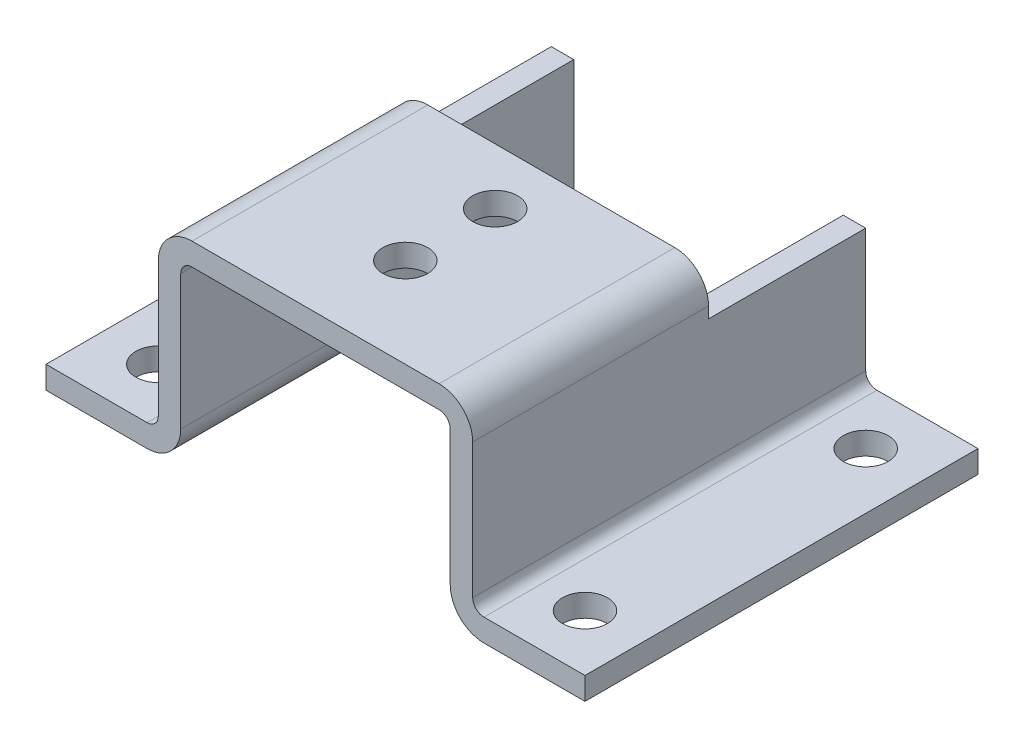
SolidWorks part; units mm, degrees
ref_plane "Front Plane" through (0, 0, 0) normal (0, 0, 1) x (1, 0, 0)
ref_plane "Top Plane" through (0, 0, 0) normal (0, 1, 0) x (1, 0, 0)
ref_plane "Right Plane" through (0, 0, 0) normal (1, 0, 0) x (0, 0, -1)
sketch "Эскиз1" plane through (0, 0, 0) normal (0, 0, 1) x (1, 0, 0)
  line L0 (0, 0) -> (9, 0)
  line L1 (12, 3) -> (12, 15)
  line L2 (13, 16) -> (35, 16)
  line L3 (36, 15) -> (36, 3)
  line L4 (39, 0) -> (48, 0)
  line L5 (48, 0) -> (48, 2)
  line L6 (48, 2) -> (39, 2)
  line L7 (38, 3) -> (38, 15)
  line L8 (35, 18) -> (13, 18)
  line L9 (10, 15) -> (10, 3)
  line L10 (9, 2) -> (0, 2)
  line L11 (0, 2) -> (0, 0)
  line L14 (24, 20.5039) -> (24, 2) construction
  arc A0 (13, 16) -> (12, 15) centre (13, 15) ccw
  arc A1 (13, 18) -> (10, 15) centre (13, 15) ccw
  arc A2 (35, 16) -> (36, 15) centre (35, 15) cw
  arc A3 (35, 18) -> (38, 15) centre (35, 15) cw
  arc A4 (9, 2) -> (10, 3) centre (9, 3) ccw
  arc A5 (9, 0) -> (12, 3) centre (9, 3) ccw
  arc A6 (39, 2) -> (38, 3) centre (39, 3) cw
  arc A7 (39, 0) -> (36, 3) centre (39, 3) cw
  point P13 (48, 1)
  dimension "D8" = 1
  dimension "D3" = 1
  dimension "D1" = 2
  dimension "D4" = 48
  dimension "D5" = 24
  dimension "D6" = 16
extrude "Бобышка-Вытянуть1" add sketch "Эскиз1" along normal blind 35
sketch "Эскиз2" plane through (0, 18, 0) normal (0, 1, 0) x (1, 0, 0)
  line L0 (0, 0) -> (48, 0)
  line L1 (0, 0) -> (0, -14)
  line L2 (48, 0) -> (48, -14)
  line L3 (0, -14) -> (48, -14)
  dimension "D1" = 48
  dimension "D2" = 14
extrude "Вырез-Вытянуть1" cut sketch "Эскиз2" against normal blind 4
sketch "Эскиз3" plane through (0, 18, 0) normal (0, 1, 0) x (1, 0, 0)
  line L0 (24, -14) -> (24, -35) construction
  line L1 (13, -14) -> (35, -14) construction
  line L2 (35, -35) -> (13, -35) construction
  line L3 (9, 0) -> (0, 0) construction
  circle A0 centre (24, -19) radius 2
  circle A1 centre (24, -27) radius 2
  circle A2 centre (5, -30) radius 2
  circle A3 centre (5, -5) radius 2
  circle A4 centre (43, -30) radius 2
  circle A5 centre (43, -5) radius 2
  dimension "D1" = 4
  dimension "D4" = 4
  dimension "D2" = 8
  dimension "D3" = 16
  dimension "D5" = 38
  dimension "D6" = 19
  dimension "D7" = 5
  dimension "D8" = 25
extrude "Вырез-Вытянуть2" cut sketch "Эскиз3" against normal through all
